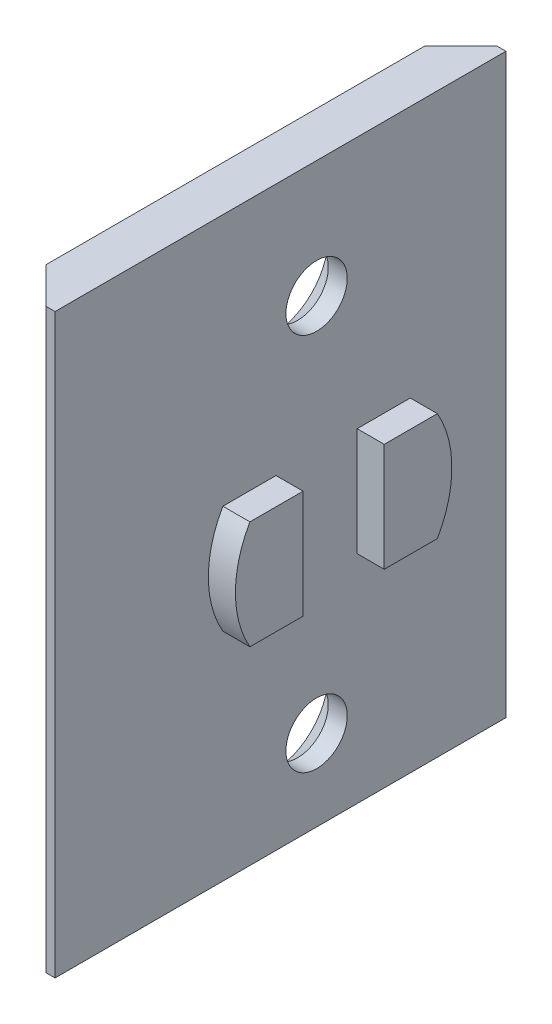
SolidWorks part; units mm, degrees
material "Сталь"
ref_plane "Спереди" through (0, 0, 0) normal (0, 0, 1) x (1, 0, 0)
ref_plane "Сверху" through (0, 0, 0) normal (0, 1, 0) x (1, 0, 0)
ref_plane "Справа" through (0, 0, 0) normal (1, 0, 0) x (0, 0, -1)
sketch "Эскиз1" plane through (0, 0, 0) normal (1, 0, 0) x (0, 0, -1)
  line L1 (-12.5, -16) -> (12.5, -16)
  line L2 (-12.5, -16) -> (-12.5, 16)
  line L3 (-12.5, 16) -> (12.5, 16)
  line L4 (12.5, -16) -> (12.5, 16)
  line L5 (-12.5, -16) -> (12.5, 16) construction
  line L6 (-12.5, 16) -> (12.5, -16) construction
  point P0 (0, 0)
  dimension "D1" = 25
  dimension "D2" = 32
extrude "Бобышка-Вытянуть1" add sketch "Эскиз1" along normal blind 2.5
chamfer "Фаска1" distance 2 angle 45 2 edges at (0, 0, 12.5) (0, 0, -12.5)
sketch "Эскиз2" plane through (0, 0, 0) normal (1, 0, 0) x (0, 0, -1)
  point P0 (2, 9.5)
  point P1 (2, -11.5)
hole_wizard "Зенковка для  винта с плоской головкой M31" positions "Трехмерный эскиз1" profile "Эскиз3" countersink size "M3" standard "Ansi Metric" end condition through all
sketch3d "Трехмерный эскиз1"
  point P0 (0, -11.5, -2)
  point P3 (0, 9.5, -2)
sketch "Эскиз3" plane through (0, -11.5, -2) normal (0, 1, 0) x (0, 0, 1)
  line L0 (0, 0) -> (0, 2.5)
  line L1 (0, 2.5) -> (1.7, 2.5)
  line L2 (1.7, 2.5) -> (1.7, 1.45)
  line L3 (1.7, 1.45) -> (3.15, 0)
  line L5 (3.15, 0) -> (0, 0)
  line L6 (-1.7, 1.45) -> (-3.15, 0) construction
  line L11 (0, -6.35) -> (0, 107.95) construction
  dimension "Диаметр сквозного отверстия" = 3.4
  dimension "Глубина сквозного отверстия" = 2.5
  dimension "Диаметр передней зенковки" = 6.3
  dimension "Угол передней зенковки" = 90
sketch "Эскиз4" plane through (2.5, 0, 0) normal (1, 0, 0) x (0, 0, -1)
  line L1 (-0.25, -3.681) -> (4.25, -3.681)
  line L2 (-0.25, -3.681) -> (-0.25, 1.681)
  line L3 (-0.25, 1.681) -> (4.25, 1.681)
  line L4 (4.25, -3.681) -> (4.25, 1.681)
  line L5 (-0.25, -3.681) -> (4.25, 1.681) construction
  line L6 (-0.25, 1.681) -> (4.25, -3.681) construction
  circle A0 centre (2, -1) radius 6
  circle A1 centre (2, -1) radius 3.5
  dimension "D1" = 12
  dimension "D2" = 7
extrude "Бобышка-Вытянуть2" add sketch "Эскиз4" along normal blind 1.5 contours A0 A1 | L2 A1 | L4 A1
sketch "Эскиз5" plane through (4, 0, 0) normal (1, 0, 0) x (0, 0, -1)
  line L0 (4.25, -3.681) -> (4.25, 1.681) construction
  line L1 (-0.25, -9) -> (4.25, -9)
  line L2 (-0.25, -9) -> (-0.25, 7)
  line L3 (-0.25, 7) -> (4.25, 7)
  line L4 (4.25, -9) -> (4.25, 7)
  line L5 (-0.25, -9) -> (4.25, 7) construction
  line L6 (-0.25, 7) -> (4.25, -9) construction
  point P0 (2, -1)
  dimension "D1" = 16
extrude "Вырез-Вытянуть1" cut sketch "Эскиз5" against normal up to surface (1.5 mm away) up to face at (2.5, 0, 0)
sketch "Эскиз6" plane through (4, 0, 0) normal (1, 0, 0) x (0, 0, -1)
  line L1 (-3.1962, -4) -> (7.1962, -4)
  line L2 (-3.1962, -4) -> (-3.1962, 2)
  line L3 (-3.1962, 2) -> (7.1962, 2)
  line L4 (7.1962, -4) -> (7.1962, 2)
  line L5 (-3.1962, -4) -> (7.1962, 2) construction
  line L6 (-3.1962, 2) -> (7.1962, -4) construction
  circle A0 centre (2, -1) radius 6
  arc A2 (4.25, -6.5621) -> (4.25, 4.5621) centre (2, -1) ccw construction
  line M1 (4.25, 4.5621) -> (4.25, -6.5621)
  arc M2 (4.25, -6.5621) -> (4.25, 4.5621) centre (2, -1) ccw
  dimension "D1" = 6
extrude "Вырез-Вытянуть2" cut sketch "Эскиз6" against normal up to surface (1.5 mm away) contours A0 L3 M1 | L3 M1 M2 | L1 A0 M1 | L1 M1 M2 up to face at (2.5, -1, 2.125)
